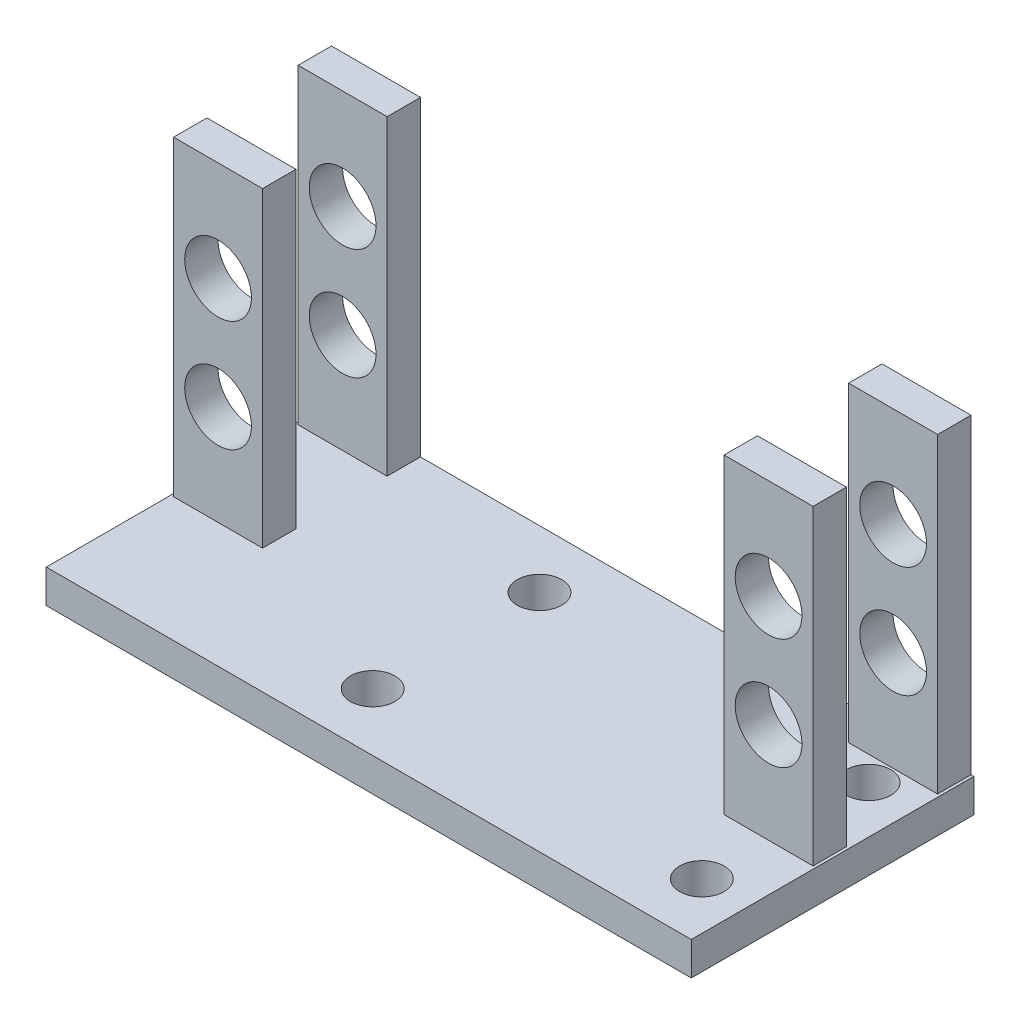
SolidWorks part; units mm, degrees
ref_plane "Front" through (0, 0, 0) normal (0, 0, 1) x (1, 0, 0)
ref_plane "Top" through (0, 0, 0) normal (0, 1, 0) x (1, 0, 0)
ref_plane "Right" through (0, 0, 0) normal (1, 0, 0) x (0, 0, -1)
sketch "草图1" plane through (0, 0, 0) normal (0, 1, 0) x (1, 0, 0)
  line L0 (0, 0) -> (0, 12.7) construction
  line L1 (0, 0) -> (0, -12.7) construction
  line L2 (0, 0) -> (29, 0) construction
  line L3 (-29, 12.7) -> (29, 12.7)
  line L4 (29, 12.7) -> (29, -12.7)
  line L5 (-29, 12.7) -> (-29, -12.7)
  line L6 (-29, -12.7) -> (29, -12.7)
  point P10 (-29, 0)
extrude "凸台-拉伸1" add sketch "草图1" along normal blind 3
sketch "草图2" plane through (0, 3, 0) normal (0, 1, 0) x (1, 0, 0)
  line L0 (0, 12.7) -> (24.75, 12.7) construction
  line L1 (29, 12.7) -> (-29, 12.7) construction
  line L2 (0, 12.7) -> (-24.75, 12.7) construction
  line L3 (-24.75, 12.7) -> (-24.75, 9.7) construction
  line L4 (-24.75, 9.7) -> (-28.75, 9.7) construction
  line L5 (-24.75, 9.7) -> (-20.75, 9.7) construction
  line L6 (24.75, 12.7) -> (24.75, 9.7) construction
  line L7 (24.75, 9.7) -> (28.75, 9.7) construction
  line L8 (24.75, 9.7) -> (20.75, 9.7) construction
  line L9 (-20.75, 9.7) -> (-28.75, 9.7)
  line L10 (-28.75, 9.7) -> (-28.75, 12.7)
  line L11 (-28.75, 12.7) -> (-20.75, 12.7)
  line L12 (-20.75, 12.7) -> (-20.75, 9.7)
  line L13 (20.75, 9.7) -> (28.75, 9.7)
  line L14 (28.75, 9.7) -> (28.75, 12.7)
  line L15 (28.75, 12.7) -> (20.75, 12.7)
  line L16 (20.75, 12.7) -> (20.75, 9.7)
  line L17 (-20.75, 0) -> (-20.75, 1.5) construction
  line L18 (-20.75, 1.5) -> (-28.75, 1.5) construction
  line L19 (-28.75, 1.5) -> (-28.75, -1.5) construction
  line L20 (-28.75, -1.5) -> (-20.75, -1.5) construction
  line L21 (-20.75, -1.5) -> (-20.75, 0) construction
  line L22 (0, 0) -> (0, 4.2412) construction
  line L23 (-28.75, 1.5) -> (-20.75, 1.5)
  line L24 (-20.75, 1.5) -> (-20.75, -1.5)
  line L25 (-20.75, -1.5) -> (-28.75, -1.5)
  line L26 (-28.75, -1.5) -> (-28.75, 1.5)
  line L27 (28.75, -1.5) -> (28.75, 1.5)
  line L28 (20.75, -1.5) -> (28.75, -1.5)
  line L29 (20.75, 1.5) -> (20.75, -1.5)
  line L30 (28.75, 1.5) -> (20.75, 1.5)
extrude "凸台-拉伸2" add sketch "草图2" along normal blind 28
sketch "草图3" plane through (0, 0, -9.7) normal (0, 0, 1) x (1, 0, 0)
  line L0 (-24.75, 17) -> (-20.75, 17) construction
  line L2 (-24.75, 17) -> (-24.75, 22) construction
  line L3 (-20.75, 31) -> (-20.75, 3) construction
  line L4 (-24.75, 17) -> (-24.75, 12) construction
  line L5 (0, 0) -> (0, 3) construction
  line L6 (-29, 3) -> (29, 3) construction
  circle A0 centre (-24.75, 12) radius 3
  circle A1 centre (-24.75, 22) radius 3
  circle A2 centre (24.75, 12) radius 3
  circle A3 centre (24.75, 22) radius 3
extrude "切除-拉伸1" cut sketch "草图3" against normal mid plane 24
sketch "草图4" plane through (0, 3, 0) normal (0, 1, 0) x (1, 0, 0)
  line L0 (0, 0) -> (24.75, 0) construction
  line L1 (24.75, 0) -> (24.75, 12.7) construction
  line L2 (28.75, 12.7) -> (20.75, 12.7) construction
  line L3 (24.75, 12.7) -> (9.95, 12.7) construction
  line L4 (20.75, 12.7) -> (-20.75, 12.7) construction
  line L5 (9.95, 12.7) -> (9.95, 0) construction
  line L6 (9.95, 0) -> (9.95, -12.7) construction
  line L7 (-29, -12.7) -> (29, -12.7) construction
  line L8 (9.95, 6.35) -> (-4.85, 6.35) construction
  line L9 (24.75, 0) -> (24.75, -7.5) construction
  circle A4 centre (24.75, -7.5) radius 2
  circle A5 centre (24.75, 7.5) radius 2
  circle A6 centre (-4.85, 7.5) radius 2
  circle A7 centre (-4.85, -7.5) radius 2
extrude "切除-拉伸2" cut sketch "草图4" against normal blind 22
